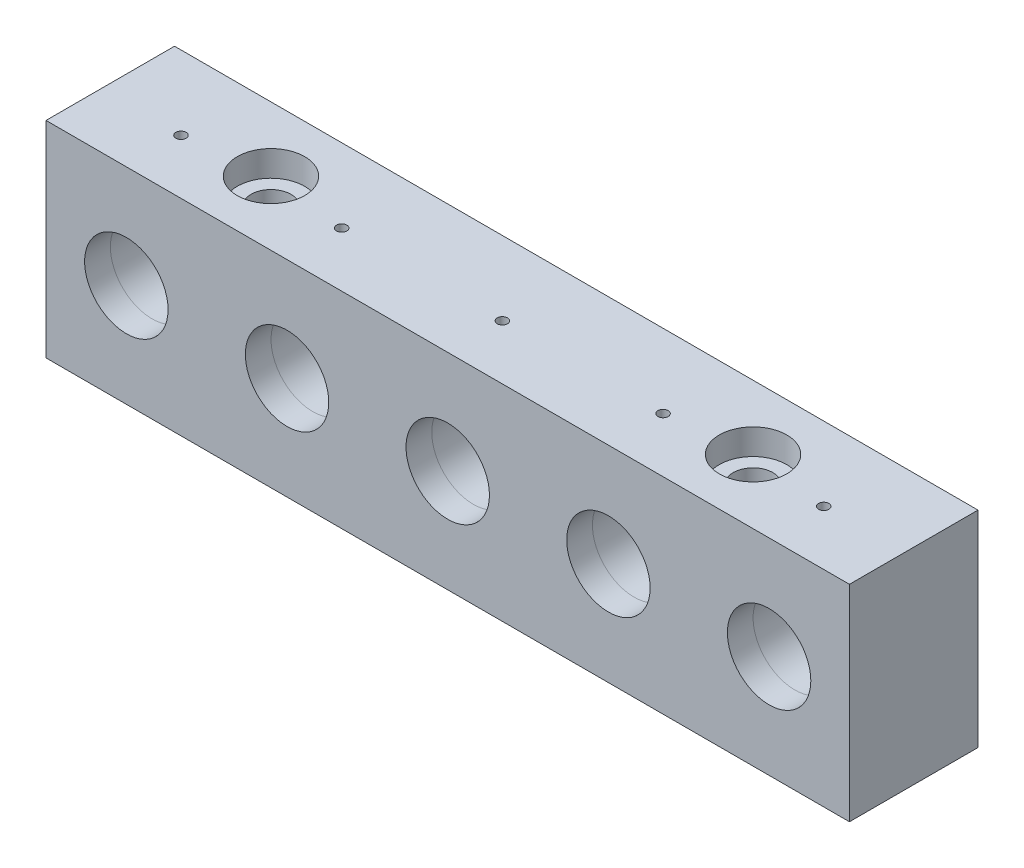
SolidWorks part; units mm, degrees
ref_plane "Front Plane" through (0, 0, 0) normal (0, 0, 1) x (1, 0, 0)
ref_plane "Top Plane" through (0, 0, 0) normal (0, 1, 0) x (1, 0, 0)
ref_plane "Right Plane" through (0, 0, 0) normal (1, 0, 0) x (0, 0, -1)
sketch "Sketch1" plane through (0, 0, 0) normal (0, 1, 0) x (1, 0, 0)
  line L1 (0, 0) -> (125, 0)
  line L2 (0, 0) -> (0, 20)
  line L3 (0, 20) -> (125, 20)
  line L4 (125, 0) -> (125, 20)
  dimension "D1" = 125
  dimension "D2" = 20
extrude "Boss-Extrude1" add sketch "Sketch1" along normal blind 32
sketch "Sketch2" plane through (0, 0, 0) normal (0, 0, 1) x (1, 0, 0)
  line L0 (0, 32) -> (0, 0) construction
  line L1 (0, 0) -> (125, 0) construction
  circle A0 centre (12.5, 16) radius 6.4897
  point P4 (0, 0)
  dimension "D2" = 12.9794
  dimension "D1" = 12.5
  dimension "D3" = 16
extrude "Cut-Extrude1" cut sketch "Sketch2" against normal blind 4
sketch "Sketch3" plane through (0, 0, -4) normal (0, 0, 1) x (1, 0, 0)
  circle A0 centre (12.5, 16) radius 6.5
  dimension "D1" = 13
extrude "Cut-Extrude2" cut sketch "Sketch3" against normal blind 6.5
hole_wizard "M12x0.5 Tapped Hole1" positions "Sketch5" profile "Sketch6" tap size "M12x0.5" standard "DIN"
sketch "Sketch5" plane through (0, 0, -10.5) normal (0, 0, 1) x (1, 0, 0)
  point P0 (12.5, 16)
sketch "Sketch6" plane through (12.5, 16, -10.5) normal (1, 0, 0) x (0, -1, 0)
  line L0 (0, 0) -> (0, 7.4549)
  line L1 (0, 7.4549) -> (5.75, 4)
  line L2 (5.75, 4) -> (5.75, 0)
  line L5 (5.75, 0) -> (0, 0)
  line L10 (0, 7.4549) -> (-5.75, 4) construction
  line L11 (0, -6.35) -> (0, 107.95) construction
  dimension "Tap Drill Dia." = 11.5
  dimension "Tap Drill Depth" = 4
  dimension "Drill Angle" = 118
cosmetic thread "Hole Thread1" parameters "D1"=4, "D2"=12
sketch "Sketch8" plane through (0, 0, 0) normal (0, 0, 1) x (1, 0, 0)
  circle A0 centre (12.5, 16) radius 2.1
  dimension "D1" = 4.2
extrude "Cut-Extrude4" cut sketch "Sketch8" against normal up to next
sketch "Sketch9" plane through (0, 0, -20) normal (0, 0, -1) x (-1, 0, 0)
  circle A0 centre (-12.5, 16) radius 2.825
  dimension "D1" = 5.65
extrude "Cut-Extrude5" cut sketch "Sketch9" against normal blind 1.1
hole_wizard "M3x0.5 Tapped Hole1" positions "Sketch10" profile "Sketch11" tap size "M3x0.5" standard "ANSI Metric"
sketch "Sketch10" plane through (0, 0, -20) normal (0, 0, -1) x (-1, 0, 0)
  line L0 (-125, 0) -> (0, 0) construction
  circle A1 centre (-12.5, 16) radius 2.825 construction
  point P0 (-19.5, 16)
  point P2 (-5.5, 16)
  point P5 (0, 0)
  point P12 (-10.3261, 17.8041)
  dimension "D2" = 7
  dimension "D3" = 7
  dimension "D1" = 16
sketch "Sketch11" plane through (19.5, 16, -20) normal (1, 0, 0) x (0, 1, 0)
  line L0 (0, 0) -> (0, 5.2511)
  line L1 (0, 5.2511) -> (1.25, 4.5)
  line L2 (1.25, 4.5) -> (1.25, 0)
  line L5 (1.25, 0) -> (0, 0)
  line L10 (0, 5.2511) -> (-1.25, 4.5) construction
  line L11 (0, -6.35) -> (0, 107.95) construction
  dimension "Tap Drill Dia." = 2.5
  dimension "Tap Drill Depth" = 4.5
  dimension "Drill Angle" = 118
cosmetic thread "Hole Thread2" parameters "D1"=3, "D2"=3
cosmetic thread "Hole Thread3" parameters "D1"=3, "D2"=3
pattern_linear "LPattern1" count 5 spacing 25 along (1, 0, 0) of "Cut-Extrude1", "Cut-Extrude2", "M12x0.5 Tapped Hole1", "Cut-Extrude4", "Cut-Extrude5", "M3x0.5 Tapped Hole1"
hole_wizard "M2 Tapped Hole1" positions "Sketch12" profile "Sketch13" tap size "M2" standard "DIN"
sketch "Sketch12" plane through (0, 32, 0) normal (0, 1, 0) x (1, 0, 0)
  line L0 (0, 0) -> (125, 0) construction
  line L1 (0, 20) -> (0, 0) construction
  point P0 (12.5, 8.5)
  point P2 (37.5, 8.5)
  point P4 (62.5, 8.5)
  point P6 (87.5, 8.5)
  point P8 (112.5, 8.5)
  point P11 (0, 0)
  dimension "D1" = 8.5
  dimension "D2" = 12.5
  dimension "D3" = 25
  dimension "D4" = 25
  dimension "D5" = 25
  dimension "D6" = 25
sketch "Sketch13" plane through (12.5, 32, -8.5) normal (1, 0, 0) x (0, 0, 1)
  line L0 (0, 0) -> (0, 9.5)
  line L1 (0, 9.5) -> (0.8, 9.5)
  line L2 (0.8, 9.5) -> (0.8, 0)
  line L5 (0.8, 0) -> (0, 0)
  line L11 (0, -6.35) -> (0, 107.95) construction
  dimension "Thru Tap Drill Dia." = 1.6
  dimension "Thru Tap Drill Depth" = 9.5
cosmetic thread "Hole Thread4" parameters "D2"=2
cosmetic thread "Hole Thread5" parameters "D2"=2
cosmetic thread "Hole Thread6" parameters "D2"=2
cosmetic thread "Hole Thread7" parameters "D2"=2
cosmetic thread "Hole Thread8" parameters "D2"=2
hole_wizard "CBORE for M6 Hex Socket Head Cap Screw1" positions "Sketch14" profile "Sketch15" counterbore size "M6" standard "DIN" end condition up to next
sketch "Sketch14" plane through (0, 32, 0) normal (0, 1, 0) x (1, 0, 0)
  line L0 (0, 20) -> (0, 0) construction
  line L1 (125, 0) -> (125, 20) construction
  line L2 (0, 0) -> (125, 0) construction
  point P0 (25, 10)
  point P2 (100, 10)
  point P11 (0, 0)
  point P12 (0, 0)
  dimension "D1" = 25
  dimension "D2" = 25
  dimension "D3" = 10
sketch "Sketch15" plane through (25, 32, -10) normal (1, 0, 0) x (0, 0, 1)
  line L0 (0, 0) -> (0, 32)
  line L1 (0, 32) -> (3.1, 32)
  line L3 (3.1, 32) -> (3.1, 4)
  line L4 (3.1, 4) -> (5.25, 4)
  line L5 (5.25, 4) -> (5.25, 0)
  line L7 (5.25, 0) -> (0, 0)
  line L11 (0, -6.35) -> (0, 107.95) construction
  dimension "Thru Hole Dia." = 6.2
  dimension "Thru Hole Depth" = 32
  dimension "C'Bore Dia." = 10.5
  dimension "C'Bore Depth" = 4
